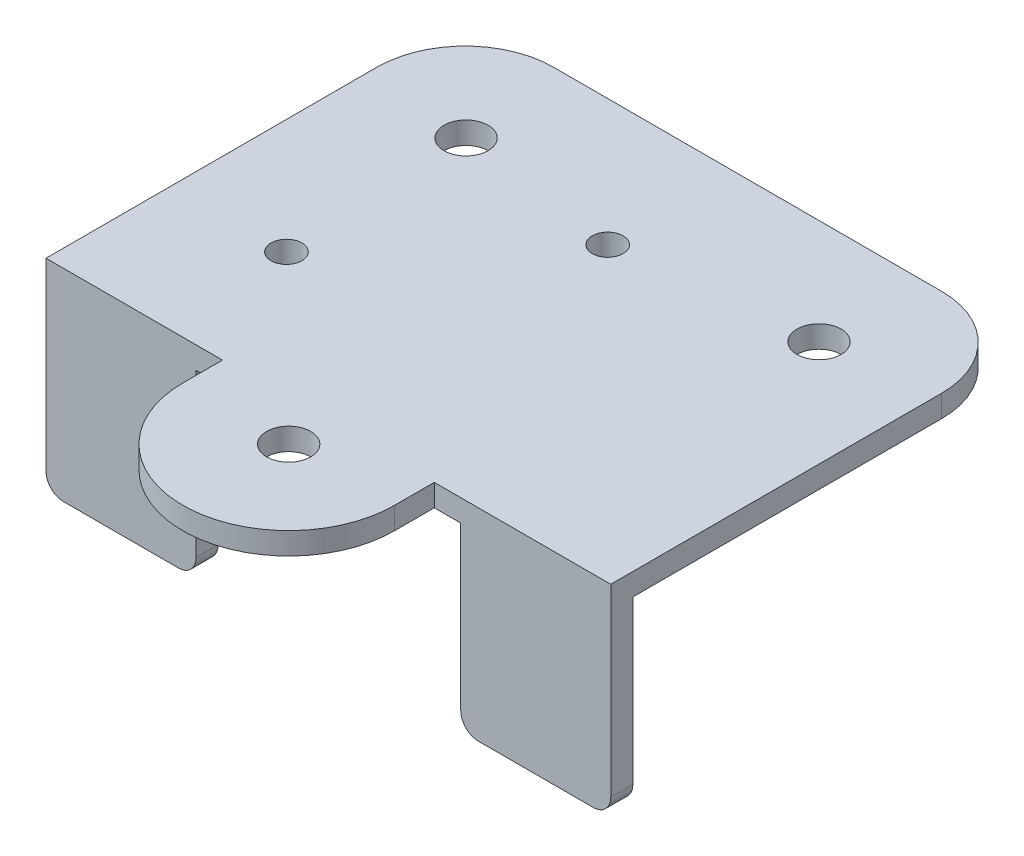
SolidWorks part; units mm, degrees
ref_plane "Front Plane" through (0, 0, 0) normal (0, 0, 1) x (1, 0, 0)
ref_plane "Top Plane" through (0, 0, 0) normal (0, 1, 0) x (1, 0, 0)
ref_plane "Right Plane" through (0, 0, 0) normal (1, 0, 0) x (0, 0, -1)
sketch "Sketch2" plane through (0, 0, 0) normal (0, 1, 0) x (1, 0, 0)
  line L1 (-32, 23.75) -> (32, 23.75)
  line L2 (-32, 23.75) -> (-32, -23.75)
  line L3 (-32, -23.75) -> (32, -23.75)
  line L4 (32, 23.75) -> (32, -23.75)
  line L5 (-32, 23.75) -> (32, -23.75) construction
  line L6 (-32, -23.75) -> (32, 23.75) construction
  circle A0 centre (-1.5, 9.4) radius 1.75
  circle A1 centre (-19, -9.5) radius 1.75
  point P0 (0, 0)
  dimension "D3" = 14.35
  dimension "D4" = 3.5
  dimension "D6" = 13
  dimension "D1" = 64
  dimension "D2" = 47.5
  dimension "D5" = 30.5
  dimension "D7" = 33.25
extrude "Boss-Extrude1" add sketch "Sketch2" along normal blind 2.5
fillet "Fillet1" radius 10 2 edges at (32, 1.25, -23.75) (-32, 1.25, -23.75)
sketch "Sketch3" plane through (0, 2.5, 0) normal (0, 1, 0) x (1, 0, 0)
  line L1 (-12, -28.25) -> (-12, -23.75)
  line L2 (-32, -23.75) -> (32, -23.75) construction
  line L3 (-12, -23.75) -> (12, -23.75)
  line L4 (12, -23.75) -> (12, -28.25)
  arc A0 (-12, -28.25) -> (12, -28.25) centre (0, -28.25) ccw
  circle A1 centre (0, -28.25) radius 2.5
  dimension "D1" = 5
  dimension "D2" = 24
  dimension "D3" = 4.5
extrude "Boss-Extrude2" add sketch "Sketch3" against normal up to surface (2.5 mm away) up to face at (0, 0, -5.2737)
sketch "Sketch4" plane through (0, 0, 0) normal (0, -1, 0) x (1, 0, 0)
  line L1 (-32, 23.75) -> (-15, 23.75)
  line L2 (-32, 23.75) -> (-32, 21.25)
  line L3 (-32, 21.25) -> (-15, 21.25)
  line L4 (-15, 23.75) -> (-15, 21.25)
  line L5 (32, 23.75) -> (15, 23.75)
  line L6 (32, 23.75) -> (32, 21.25)
  line L7 (32, 21.25) -> (15, 21.25)
  line L8 (15, 23.75) -> (15, 21.25)
  dimension "D1" = 2.5
  dimension "D2" = 17
extrude "Boss-Extrude3" add sketch "Sketch4" along normal blind 20.4
fillet "Fillet2" radius 2 4 edges at (-32, -20.4, 22.5) (-15, -20.4, 22.5) (15, -20.4, 22.5) (32, -20.4, 22.5)
sketch "Sketch5" plane through (0, 2.5, 0) normal (0, 1, 0) x (1, 0, 0)
  line L0 (-20, 11.85) -> (-20, 23.75) construction
  line L1 (22, 23.75) -> (-22, 23.75) construction
  line L2 (-32, 13.75) -> (-32, -23.75) construction
  line L3 (32, -23.75) -> (32, 13.75) construction
  circle A0 centre (-20, 11.85) radius 2.5
  circle A1 centre (20, 11.85) radius 2.5
  point P9 (0, 0)
  dimension "D1" = 5
  dimension "D2" = 11.9
  dimension "D3" = 12
  dimension "D4" = 12
extrude "Cut-Extrude1" cut sketch "Sketch5" against normal through all
